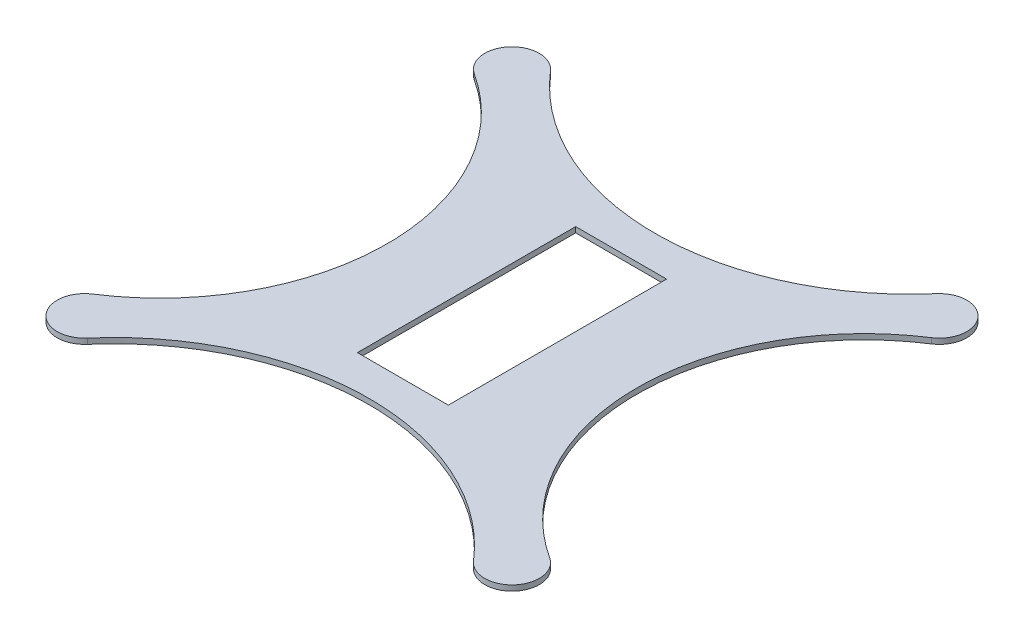
SolidWorks part; units mm, degrees
ref_plane "Front" through (0, 0, 0) normal (0, 0, 1) x (1, 0, 0)
ref_plane "Top" through (0, 0, 0) normal (0, 1, 0) x (1, 0, 0)
ref_plane "Right" through (0, 0, 0) normal (1, 0, 0) x (0, 0, -1)
sketch "Sketch4" plane through (0, 0, 0) normal (0, 1, 0) x (1, 0, 0)
  line L0 (0, 0) -> (0, 354.5375) construction
  line L1 (25, -60) -> (-25, -60)
  line L2 (25, -60) -> (25, 60)
  line L3 (25, 60) -> (-25, 60)
  line L4 (-25, -60) -> (-25, 60)
  line L5 (25, -60) -> (-25, 60) construction
  line L6 (25, 60) -> (-25, -60) construction
  line L11 (25, 60) -> (117.5, 117.5) construction
  line L12 (-117.5, 117.5) -> (-25, 60) construction
  line L13 (0, 0) -> (249.298, 0) construction
  line L14 (25, -60) -> (117.5, -117.5) construction
  line L15 (-117.5, -117.5) -> (-25, -60) construction
  line L16 (-117.5, -117.5) -> (-117.5, 117.5) construction
  line L17 (-117.5, 117.5) -> (117.5, 117.5) construction
  line L18 (117.5, 117.5) -> (117.5, -117.5) construction
  line L19 (117.5, -117.5) -> (-117.5, -117.5) construction
  line L20 (0, -78.5878) -> (0, 78.5878) construction
  arc A0 (-106.129, 127.2827) -> (-125.6554, 104.9107) centre (-117.5, 117.5) ccw
  arc A1 (125.6554, 104.9107) -> (106.129, 127.2827) centre (117.5, 117.5) ccw
  arc A2 (-125.6554, -104.9107) -> (-106.129, -127.2827) centre (-117.5, -117.5) ccw
  arc A3 (106.129, -127.2827) -> (125.6554, -104.9107) centre (117.5, -117.5) ccw
  arc A7 (-106.129, 127.2827) -> (106.129, 127.2827) centre (0, 218.5878) ccw
  arc A8 (125.6554, 104.9107) -> (125.6554, -104.9107) centre (193.6167, 0) ccw
  arc A11 (-106.129, -127.2827) -> (106.129, -127.2827) centre (0, -218.5878) cw
  arc A12 (-125.6554, 104.9107) -> (-125.6554, -104.9107) centre (-193.6167, 0) cw
  point P0 (0, 0)
  point P6 (0, 0)
  point P11 (0, 0)
  point P12 (0, 0)
  dimension "D5" = 30
  dimension "D6" = 30
  dimension "D7" = 30
  dimension "D8" = 30
  dimension "D9" = 125
  dimension "D10" = 140
  dimension "D11" = 125
  dimension "D1" = 50
  dimension "D2" = 120
  dimension "D3" = 235
  dimension "D4" = 235
extrude "Boss-Extrude1" add sketch "Sketch4" along normal blind 3
